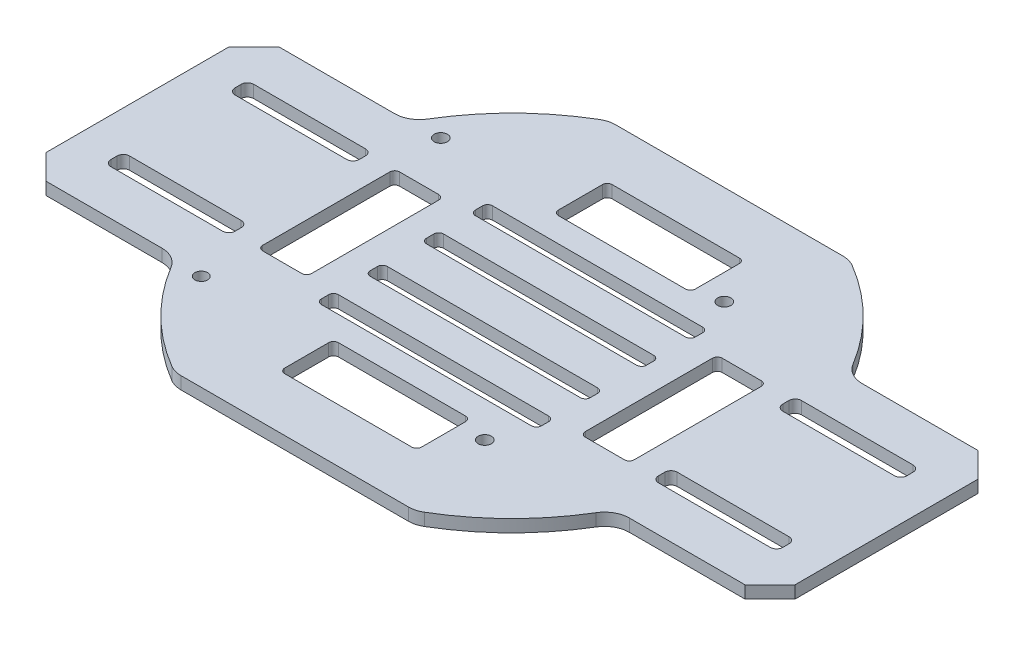
SolidWorks part; units mm, degrees
ref_plane "Front Plane" through (0, 0, 0) normal (0, 0, 1) x (1, 0, 0)
ref_plane "Top Plane" through (0, 0, 0) normal (0, 1, 0) x (1, 0, 0)
ref_plane "Right Plane" through (0, 0, 0) normal (1, 0, 0) x (0, 0, -1)
sketch "Sketch1" plane through (0, 0, 0) normal (0, 1, 0) x (1, 0, 0)
  line L0 (0, -1000) -> (0, 49000) construction
  line L1 (-23.2448, 44.45) -> (23.2448, 44.45)
  line L2 (-76.5969, 18.7325) -> (-76.5969, -18.7325)
  line L3 (-23.2448, -44.45) -> (23.2448, -44.45)
  line L4 (76.5969, 18.7325) -> (76.5969, -18.7325)
  line L6 (35.4178, 36.4243) -> (41.9684, 29.8736) construction
  line L7 (-76.5969, 0) -> (76.5969, 0) construction
  line L8 (-71.5169, 23.8125) -> (-47.8309, 23.8125)
  line L9 (-71.5169, -23.8125) -> (-47.8309, -23.8125)
  line L10 (-23.8125, 64.7529) -> (-23.8125, -44.45) construction
  line L11 (23.8125, 64.7529) -> (23.8125, -44.45) construction
  line L12 (47.8309, -23.8125) -> (71.5169, -23.8125)
  line L13 (47.8309, 23.8125) -> (71.5169, 23.8125)
  line L14 (-76.5969, -18.7325) -> (-71.5169, -23.8125)
  line L15 (-71.5169, 23.8125) -> (-76.5969, 18.7325)
  line L16 (71.5169, 23.8125) -> (76.5969, 18.7325)
  line L17 (71.5169, -23.8125) -> (76.5969, -18.7325)
  line L18 (707.1068, -707.1068) -> (-34648.2323, 34648.2323) construction
  line L19 (-707.1068, -707.1068) -> (34648.2323, 34648.2323) construction
  circle A0 centre (0, 0) radius 6.35 construction
  arc A1 (-25.8276, 43.7444) -> (-43.4827, 26.2659) centre (0, 0) ccw
  arc A2 (25.8276, 43.7444) -> (23.2448, 44.45) centre (23.2448, 39.37) ccw
  arc A3 (-23.2448, 44.45) -> (-25.8276, 43.7444) centre (-23.2448, 39.37) ccw
  arc A4 (25.8276, -43.7444) -> (43.4827, -26.2659) centre (0, 0) ccw
  arc A5 (25.8276, -43.7444) -> (23.2448, -44.45) centre (23.2448, -39.37) cw
  arc A6 (-25.8276, -43.7444) -> (-23.2448, -44.45) centre (-23.2448, -39.37) ccw
  arc A7 (-43.4827, -26.2659) -> (-25.8276, -43.7444) centre (0, 0) ccw
  arc A8 (43.4827, 26.2659) -> (25.8276, 43.7444) centre (0, 0) ccw
  arc A9 (-47.8309, -23.8125) -> (-43.4827, -26.2659) centre (-47.8309, -28.8925) cw
  arc A10 (47.8309, -23.8125) -> (43.4827, -26.2659) centre (47.8309, -28.8925) ccw
  arc A11 (43.4827, 26.2659) -> (47.8309, 23.8125) centre (47.8309, 28.8925) ccw
  arc A12 (-47.8309, 23.8125) -> (-43.4827, 26.2659) centre (-47.8309, 28.8925) ccw
  point P0 (0, 0)
  point P8 (76.5969, -23.8125)
  point P11 (-76.5969, -23.8125)
  point P12 (-76.5969, 23.8125)
  point P34 (76.5969, 23.8125)
  point P81 (0, 0)
  dimension "D3" = 12.7
  dimension "D6" = 5.08
  dimension "D1" = 5.08
  dimension "D2" = 5.08
  dimension "D4" = 23.8125
  dimension "D5" = 23.8125
extrude "Boss-Extrude1" add sketch "Sketch1" along normal blind 2.54
sketch "Sketch3" plane through (0, 2.54, 0) normal (0, 1, 0) x (1, 0, 0)
  line L0 (0, -61.6163) -> (0, 61.6163) construction
  line L1 (-109.9353, 0) -> (109.9353, 0) construction
  line L2 (-14, -28) -> (14, -28) construction
  line L3 (-14, 33.5) -> (14, 33.5)
  line L4 (-14, 33.5) -> (-14, 22.5)
  line L5 (-14, 22.5) -> (14, 22.5)
  line L6 (14, 33.5) -> (14, 22.5)
  line L7 (0, 22.5) -> (0, 33.5) construction
  line L8 (-14, 28) -> (14, 28) construction
  line L9 (0, -22.5) -> (0, -33.5) construction
  line L10 (14, -33.5) -> (14, -22.5)
  line L11 (-14, -22.5) -> (14, -22.5)
  line L12 (-14, -33.5) -> (-14, -22.5)
  line L13 (-14, -33.5) -> (14, -33.5)
  line L14 (38, 0) -> (28, 0) construction
  line L15 (-38, -14) -> (-28, -14)
  line L16 (-38, -14) -> (-38, 14)
  line L17 (-38, 14) -> (-28, 14)
  line L18 (-28, -14) -> (-28, 14)
  line L19 (-33, 14) -> (-33, -14) construction
  line L20 (-38, 0) -> (-28, 0) construction
  line L21 (33, 14) -> (33, -14) construction
  line L22 (28, -14) -> (28, 14)
  line L23 (38, 14) -> (28, 14)
  line L24 (38, -14) -> (38, 14)
  line L25 (38, -14) -> (28, -14)
  point P0 (0, 28)
  point P4 (0, 0)
  point P7 (0, 0)
  point P19 (0, -28)
  point P20 (-33, 0)
  point P32 (33, 0)
  dimension "D1" = 28
  dimension "D2" = 11
  dimension "D3" = 22.5
  dimension "D4" = 10
  dimension "D5" = 28
  dimension "D6" = 28
sketch "Sketch4" plane through (0, 2.54, 0) normal (0, 1, 0) x (1, 0, 0)
  line L0 (-1000, 0) -> (49000, 0) construction
  line L1 (76.5969, -18.7325) -> (76.5969, 18.7325) construction
  line L2 (44.5929, 14.605) -> (67.4529, 14.605)
  line L3 (43.3229, 13.335) -> (43.3229, 12.065)
  line L4 (44.5929, 10.795) -> (67.4529, 10.795)
  line L5 (68.7229, 13.335) -> (68.7229, 12.065)
  line L6 (43.3229, 14.605) -> (68.7229, 10.795) construction
  line L7 (43.3229, 10.795) -> (68.7229, 14.605) construction
  line L8 (68.7229, -13.335) -> (68.7229, -12.065)
  line L9 (44.5929, -10.795) -> (67.4529, -10.795)
  line L10 (43.3229, -13.335) -> (43.3229, -12.065)
  line L11 (44.5929, -14.605) -> (67.4529, -14.605)
  line L12 (0, 0) -> (0, -50000) construction
  line L13 (-44.5929, -14.605) -> (-67.4529, -14.605)
  line L14 (-43.3229, -13.335) -> (-43.3229, -12.065)
  line L15 (-44.5929, -10.795) -> (-67.4529, -10.795)
  line L16 (-68.7229, -13.335) -> (-68.7229, -12.065)
  line L17 (-43.3229, 10.795) -> (-68.7229, 14.605) construction
  line L18 (-43.3229, 14.605) -> (-68.7229, 10.795) construction
  line L19 (-68.7229, 13.335) -> (-68.7229, 12.065)
  line L20 (-44.5929, 10.795) -> (-67.4529, 10.795)
  line L21 (-43.3229, 13.335) -> (-43.3229, 12.065)
  line L22 (-44.5929, 14.605) -> (-67.4529, 14.605)
  arc A0 (44.5929, 10.795) -> (43.3229, 12.065) centre (44.5929, 12.065) cw
  arc A1 (43.3229, 13.335) -> (44.5929, 14.605) centre (44.5929, 13.335) cw
  arc A2 (68.7229, 12.065) -> (67.4529, 10.795) centre (67.4529, 12.065) cw
  arc A3 (68.7229, 13.335) -> (67.4529, 14.605) centre (67.4529, 13.335) ccw
  arc A4 (68.7229, -12.065) -> (67.4529, -10.795) centre (67.4529, -12.065) ccw
  arc A5 (68.7229, -13.335) -> (67.4529, -14.605) centre (67.4529, -13.335) cw
  arc A6 (44.5929, -10.795) -> (43.3229, -12.065) centre (44.5929, -12.065) ccw
  arc A7 (43.3229, -13.335) -> (44.5929, -14.605) centre (44.5929, -13.335) ccw
  arc A8 (-43.3229, -13.335) -> (-44.5929, -14.605) centre (-44.5929, -13.335) cw
  arc A9 (-44.5929, -10.795) -> (-43.3229, -12.065) centre (-44.5929, -12.065) cw
  arc A10 (-68.7229, -13.335) -> (-67.4529, -14.605) centre (-67.4529, -13.335) ccw
  arc A11 (-68.7229, -12.065) -> (-67.4529, -10.795) centre (-67.4529, -12.065) cw
  arc A12 (-68.7229, 13.335) -> (-67.4529, 14.605) centre (-67.4529, 13.335) cw
  arc A13 (-68.7229, 12.065) -> (-67.4529, 10.795) centre (-67.4529, 12.065) ccw
  arc A14 (-43.3229, 13.335) -> (-44.5929, 14.605) centre (-44.5929, 13.335) ccw
  arc A15 (-44.5929, 10.795) -> (-43.3229, 12.065) centre (-44.5929, 12.065) ccw
  point P1 (56.0229, 12.7)
  point P64 (-56.0229, 12.7)
  dimension "D5" = 1.27
  dimension "D1" = 25.4
  dimension "D2" = 3.81
  dimension "D3" = 7.874
  dimension "D4" = 10.795
extrude "切除-拉伸1" cut sketch "Sketch3" against normal blind 10
extrude "Cut-Extrude2" cut sketch "Sketch4" against normal blind 2.54
sketch "草图1" plane through (0, 2.54, 0) normal (0, 1, 0) x (1, 0, 0)
  line L0 (-1000, 0) -> (49000, 0) construction
  line L1 (-22.5, 7.5) -> (22.5, 7.5)
  line L2 (-22.5, 7.5) -> (-22.5, 4)
  line L3 (-22.5, 4) -> (22.5, 4)
  line L4 (22.5, 7.5) -> (22.5, 4)
  line L5 (0, 4) -> (0, 7.5) construction
  line L6 (-22.5, 5.75) -> (22.5, 5.75) construction
  line L7 (0, -1000) -> (0, 49000) construction
  line L8 (-22.5, 17.5) -> (-22.5, 14)
  line L9 (-22.5, 17.5) -> (22.5, 17.5)
  line L10 (22.5, 17.5) -> (22.5, 14)
  line L11 (-22.5, 14) -> (22.5, 14)
  line L12 (-22.5, -4) -> (22.5, -4)
  line L13 (22.5, -7.5) -> (22.5, -4)
  line L14 (-22.5, -7.5) -> (22.5, -7.5)
  line L15 (-22.5, -7.5) -> (-22.5, -4)
  line L16 (-22.5, -17.5) -> (22.5, -17.5)
  line L17 (22.5, -17.5) -> (22.5, -14)
  line L18 (-22.5, -14) -> (22.5, -14)
  line L19 (-22.5, -17.5) -> (-22.5, -14)
  point P0 (0, 5.75)
  dimension "D1" = 3.5
  dimension "D2" = 45
  dimension "D3" = 4
  dimension "D4" = 2
extrude "切除-拉伸2" cut sketch "草图1" against normal up to surface (2.54 mm away) up to face at (-56.0229, 0, -12.7)
fillet "圆角1" radius 1 32 edges at (14, 1.27, 33.5) (-14, 1.27, 33.5) (-14, 1.27, 22.5) (-28, 1.27, 14) (-38, 1.27, 14) (-28, 1.27, -14) (-38, 1.27, -14) (14, 1.27, -33.5) (14, 1.27, -22.5) (-14, 1.27, -22.5) (-14, 1.27, -33.5) (38, 1.27, -14) (38, 1.27, 14) (28, 1.27, -14) (28, 1.27, 14) (14, 1.27, 22.5) (22.5, 1.27, 17.5) (22.5, 1.27, 14) (-22.5, 1.27, 17.5) (-22.5, 1.27, 14) (22.5, 1.27, 7.5) (22.5, 1.27, 4) (-22.5, 1.27, 7.5) (-22.5, 1.27, 4) (22.5, 1.27, -4) (22.5, 1.27, -7.5) (-22.5, 1.27, -4) (-22.5, 1.27, -7.5) (22.5, 1.27, -14) (22.5, 1.27, -17.5) (-22.5, 1.27, -14) (-22.5, 1.27, -17.5)
sketch "草图2" plane through (0, 0, 0) normal (0, -1, 0) x (1, 0, 0)
  line L0 (-39.2923, -27.723) -> (39.7077, -27.723) construction
  line L1 (42.7077, -24.723) -> (42.7077, 25.277) construction
  line L2 (39.7077, 28.277) -> (-39.2923, 28.277) construction
  line L3 (-42.2923, 25.277) -> (-42.2923, -24.723) construction
  arc A0 (-42.2923, -24.723) -> (-39.2923, -27.723) centre (-39.2923, -24.723) ccw construction
  arc A1 (39.7077, -27.723) -> (42.7077, -24.723) centre (39.7077, -24.723) ccw construction
  arc A2 (42.7077, 25.277) -> (39.7077, 28.277) centre (39.7077, 25.277) ccw construction
  arc A3 (-39.2923, 28.277) -> (-42.2923, 25.277) centre (-39.2923, 25.277) ccw construction
  circle A4 centre (19.2077, -24.223) radius 1.35
  circle A5 centre (19.2077, 24.777) radius 1.35
  circle A6 centre (-38.7923, -24.223) radius 1.35
  circle A7 centre (-38.7923, 24.777) radius 1.3
extrude "切除-拉伸5" cut sketch "草图2" against normal up to surface (2.54 mm away) up to face at (0, 2.54, 15.75)
